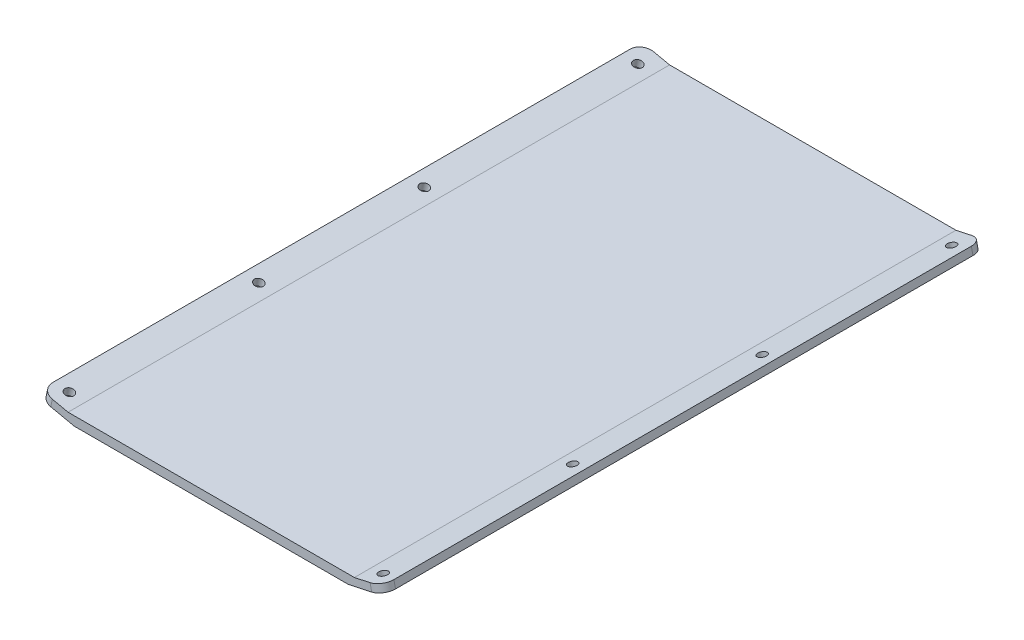
SolidWorks part; units mm, degrees
ref_plane "Front Plane" through (0, 0, 0) normal (0, 0, 1) x (1, 0, 0)
ref_plane "Top Plane" through (0, 0, 0) normal (0, 1, 0) x (1, 0, 0)
ref_plane "Right Plane" through (0, 0, 0) normal (1, 0, 0) x (0, 0, -1)
sketch "Sketch1" plane through (0, 0, 0) normal (0, 0, 1) x (1, 0, 0)
  line L0 (75.565, 0) -> (-75.565, 0)
  line L1 (-75.565, 0) -> (-90.065, 3.13)
  line L2 (0, 0) -> (0, -4.7625) construction
  line L3 (75.565, 0) -> (90.065, 3.13)
  line L4 (-90.065, 3.13) -> (-90.9044, -0.7584)
  line L5 (90.065, 3.13) -> (90.9044, -0.7584)
  line L6 (-90.9044, -0.7584) -> (-72.355, -4.7625)
  line L7 (-72.355, -4.7625) -> (72.355, -4.7625)
  line L8 (-75.565, 0) -> (-75.565, 15.2068) construction
  line L9 (90.9044, -0.7584) -> (72.355, -4.7625)
  line L11 (-75.565, 0) -> (-75.565, -4.0696) construction
  point P3 (0, 0)
  point P14 (0, -4.7625)
  dimension "D1" = 14.5
  dimension "D2" = 3.13
  dimension "D3" = 151.13
  dimension "D4" = 144.71
  dimension "D6" = 4.7625
extrude "Boss-Extrude1" add sketch "Sketch1" along normal blind 317.5
fillet "Fillet1" radius 6.35 4 edges at (-90.4847, 1.1858, 0) (90.4847, 1.1858, 0) (90.4847, 1.1858, 317.5) (-90.4847, 1.1858, 317.5)
sketch "Sketch3" plane through (-3.3643, -15.5854, 0) normal (0.211, 0.9775, 0) x (0.9775, -0.211, 0)
  line L0 (-88.6977, -311.15) -> (-88.6977, -6.35) construction
  line L1 (-73.8637, 0) -> (-82.3477, 0) construction
  line L2 (-73.8637, -317.5) -> (-73.8637, 0) construction
  line L3 (-83.6619, -9.525) -> (-78.8994, -9.525) construction
  line L6 (-81.2807, -9.525) -> (-81.2807, 0) construction
  circle A0 centre (-81.2807, -9.525) radius 2.3813
  circle A1 centre (-81.2807, -122.2375) radius 2.3813
  circle A2 centre (-81.2807, -209.55) radius 2.3813
  circle A3 centre (-81.2807, -309.5625) radius 2.3813
  dimension "D1" = 4.7625
  dimension "D2" = 112.7125
  dimension "D3" = 9.525
  dimension "D4" = 87.3125
  dimension "D5" = 100.0125
extrude "Cut-Extrude1" cut sketch "Sketch3" against normal blind 317.5
ref_plane "Plane1" through (0, 0, 158.75) normal (0, 0, -1) x (-1, 0, 0)
ref_plane "Plane2" through (0, 0, 0) normal (1, 0, 0) x (0, 0, -1)
sketch "Sketch4" plane through (3.3643, -15.5854, 0) normal (-0.211, 0.9775, 0) x (0.9775, 0.211, 0)
  line L0 (78.8994, -9.525) -> (83.6619, -9.525) construction
  line L1 (81.2807, -9.525) -> (81.2807, 0) construction
  line L2 (73.8637, -317.5) -> (73.8637, 0) construction
  line L4 (82.3477, 0) -> (73.8637, 0) construction
  line L6 (88.6977, -311.15) -> (88.6977, -6.35) construction
  circle A1 centre (81.2807, -9.525) radius 2.3813
  dimension "D1" = 4.7625
  dimension "D2" = 9.525
extrude "Cut-Extrude2" cut sketch "Sketch4" against normal blind 317.5
pattern_linear "LPattern5" count 4 spacing 100.0125 along (0, 0, 1) of "Cut-Extrude2"
